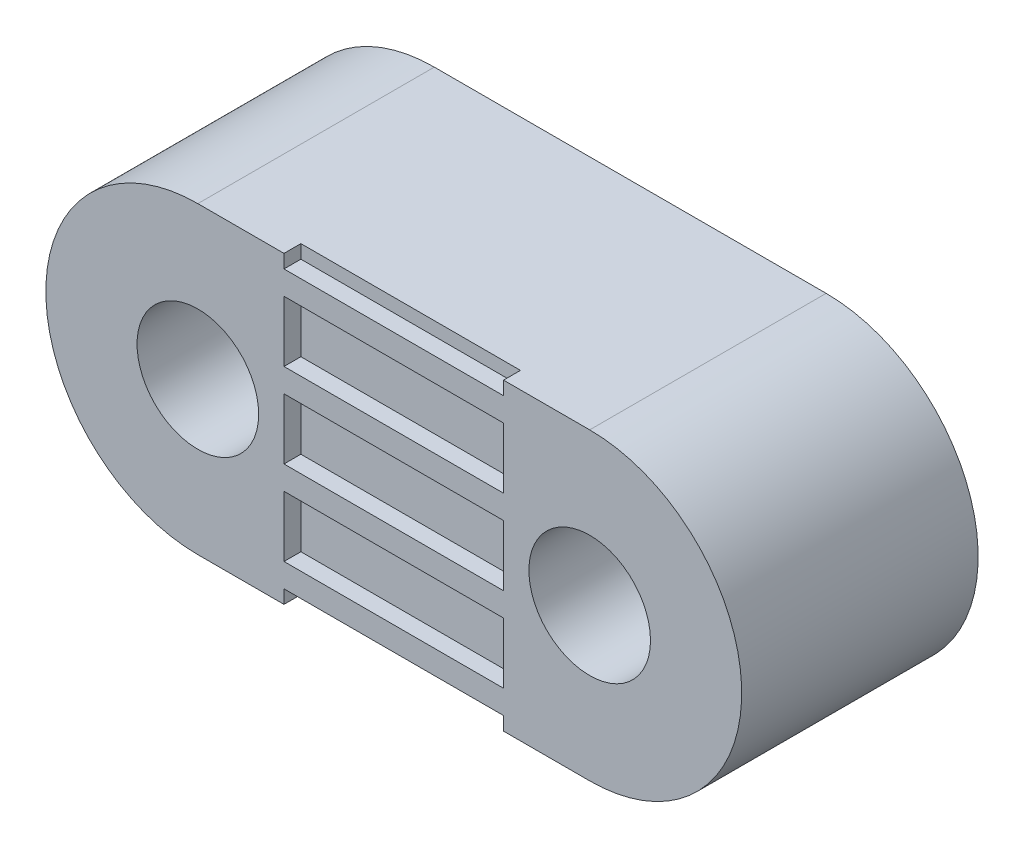
SolidWorks part; units mm, degrees
ref_plane "Front Plane" through (0, 0, 0) normal (0, 0, 1) x (1, 0, 0)
ref_plane "Top Plane" through (0, 0, 0) normal (0, 1, 0) x (1, 0, 0)
ref_plane "Right Plane" through (0, 0, 0) normal (1, 0, 0) x (0, 0, -1)
sketch "Sketch1" plane through (0, 0, 0) normal (0, 0, 1) x (1, 0, 0)
  line L1 (9, 4) -> (-2.6, 4)
  line L10 (-2.6, -5) -> (9, -5)
  arc A0 (-2.6, 4) -> (-2.6, -5) centre (-2.6, -0.5) ccw
  arc A1 (9, -5) -> (9, 4) centre (9, -0.5) ccw
extrude "Boss-Extrude1" add sketch "Sketch1" against normal blind 7
sketch "Sketch5" plane through (0, 0, 0) normal (0, 0, 1) x (1, 0, 0)
  circle A1 centre (9, -0.5) radius 1.8
  circle A3 centre (-2.6, -0.5) radius 1.8
extrude "Cut-Extrude4" cut sketch "Sketch5" against normal through all
sketch "Sketch2" plane through (0, 0, 0) normal (0, 0, 1) x (1, 0, 0)
  line L0 (-0.05, 2.9) -> (-0.05, 1.1)
  line L1 (-0.05, -5.5) -> (6.45, -5.5)
  line L2 (-0.05, 0.4) -> (-0.05, -1.4)
  line L3 (6.45, -4.6) -> (-0.05, -4.6)
  line L4 (6.45, -2.1) -> (-0.05, -2.1)
  line L5 (-0.05, -2.1) -> (-0.05, -3.9)
  line L6 (-0.05, -3.9) -> (6.45, -3.9)
  line L7 (-0.05, -4.6) -> (-0.05, -5.5)
  line L8 (6.45, 0.4) -> (-0.05, 0.4)
  line L9 (6.45, -3.9) -> (6.45, -2.1)
  line L10 (-0.05, -1.4) -> (6.45, -1.4)
  line L11 (6.45, -1.4) -> (6.45, 0.4)
  line L12 (6.45, 2.9) -> (-0.05, 2.9)
  line L13 (6.45, 1.1) -> (6.45, 2.9)
  line L14 (-0.05, 1.1) -> (6.45, 1.1)
  line L15 (6.45, 3.6) -> (6.45, 4.5)
  line L16 (6.45, 4.5) -> (-0.05, 4.5)
  line L18 (-0.05, 3.6) -> (6.45, 3.6)
  line L23 (6.45, -5.5) -> (6.45, -4.6)
  line L26 (-0.05, 4.5) -> (-0.05, 3.6)
extrude "Cut-Extrude1" cut sketch "Sketch2" against normal blind 0.5
